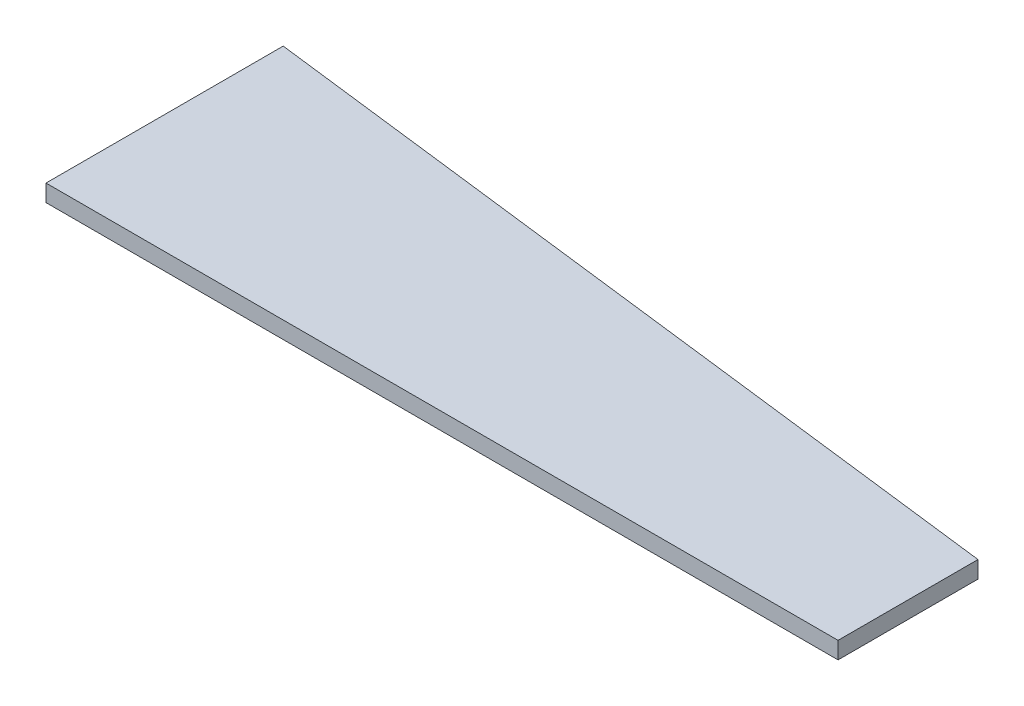
SolidWorks part; units mm, degrees
ref_plane "Front Plane" through (0, 0, 0) normal (0, 0, 1) x (1, 0, 0)
ref_plane "Top Plane" through (0, 0, 0) normal (0, 1, 0) x (1, 0, 0)
ref_plane "Right Plane" through (0, 0, 0) normal (1, 0, 0) x (0, 0, -1)
sketch "Sketch1" plane through (0, 0, 0) normal (0, 1, 0) x (1, 0, 0)
  line L0 (138.0369, -41.3388) -> (138.0369, 5.6612)
  line L2 (-127.9631, 38.3219) -> (-127.9631, -41.3388)
  line L3 (-127.9631, -41.3388) -> (138.0369, -41.3388)
  line L5 (-127.9631, 38.3219) -> (138.0369, -41.3388) construction
  line L8 (-127.9631, 38.3219) -> (138.0369, 5.6612)
  line L9 (138.0369, 5.6612) -> (-127.9631, 5.6612) construction
  point P0 (0, 0)
  dimension "D1" = 47
  dimension "D2" = 266
  dimension "D3" = 7
  dimension "D4" = 90
extrude "Boss-Extrude1" add sketch "Sketch1" along normal blind 5.7
